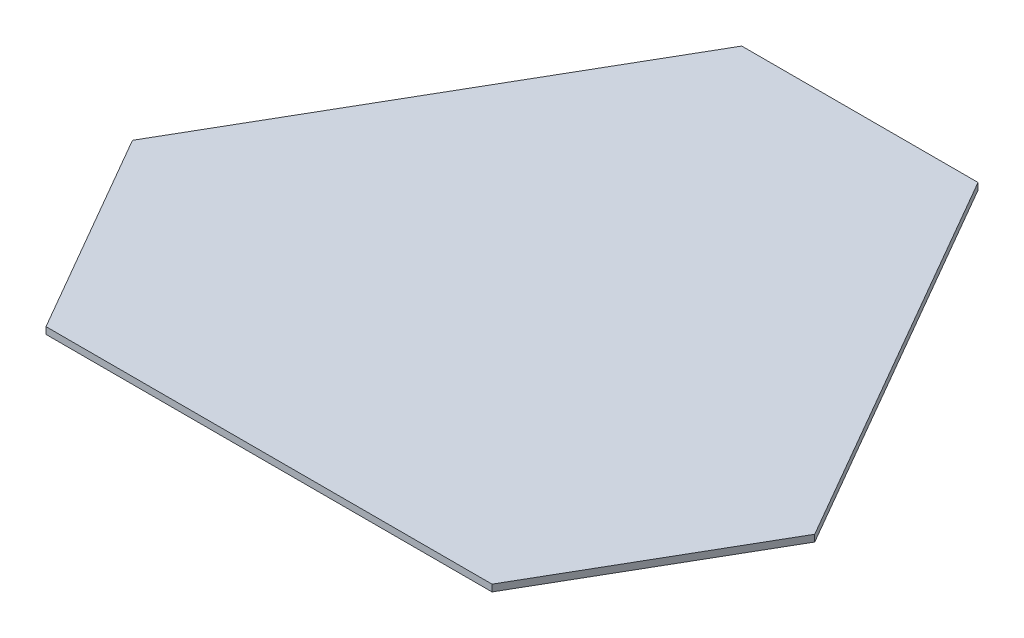
SolidWorks part; units mm, degrees
ref_plane "Front Plane" through (0, 0, 0) normal (0, 0, 1) x (1, 0, 0)
ref_plane "Top Plane" through (0, 0, 0) normal (0, 1, 0) x (1, 0, 0)
ref_plane "Right Plane" through (0, 0, 0) normal (1, 0, 0) x (0, 0, -1)
sketch "Sketch2" plane through (0, 0, 0) normal (0, 1, 0) x (1, 0, 0)
  line L0 (176.758, -114.4551) -> (26.758, 145.3525)
  line L1 (150, -160.8013) -> (-150, -160.8013)
  line L2 (-176.758, -114.4551) -> (-26.758, 145.3525)
  arc A0 (26.758, 145.3525) -> (-26.758, 145.3525) centre (0, 129.9038) ccw
  arc A1 (150, -160.8013) -> (176.758, -114.4551) centre (150, -129.9038) ccw
  arc A2 (-176.758, -114.4551) -> (-150, -160.8013) centre (-150, -129.9038) ccw
sketch "Sketch3" plane through (0, 0, 0) normal (0, 1, 0) x (1, 0, 0)
  line L0 (-176.758, -114.4551) -> (-26.758, 145.3525) construction
  line L1 (176.758, -114.4551) -> (26.758, 145.3525) construction
  line L2 (150, -160.8013) -> (-150, -160.8013) construction
  line L3 (-151.172, -70.1388) -> (-52.344, 101.0363)
  line L4 (151.172, -70.1388) -> (52.344, 101.0363)
  line L5 (98.828, -160.8013) -> (-98.828, -160.8013)
  line L6 (-151.172, -70.1388) -> (-98.828, -160.8013)
  line L7 (98.828, -160.8013) -> (151.172, -70.1388)
  line L8 (-52.344, 101.0363) -> (52.344, 101.0363)
  dimension "D1" = 60
  dimension "D2" = 60
extrude "Boss-Extrude1" add sketch "Sketch3" along normal blind 3
sketch "Sketch4" plane through (0, 3, 0) normal (0, 1, 0) x (1, 0, 0)
  line L0 (0, 101.0363) -> (0, -43.3013) construction
  line L1 (52.344, 101.0363) -> (-52.344, 101.0363) construction
  line L2 (-125, -115.4701) -> (0, -43.3013) construction
  line L3 (-151.172, -70.1388) -> (-98.828, -160.8013) construction
  line L4 (125, -115.4701) -> (0, -43.3013) construction
  line L5 (98.828, -160.8013) -> (151.172, -70.1388) construction
